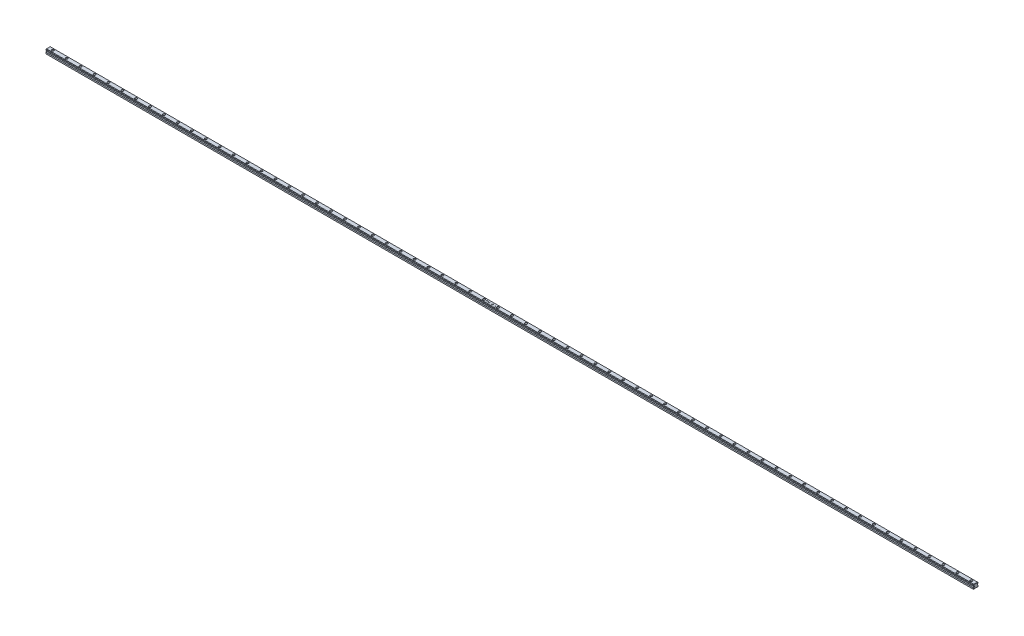
SolidWorks part; units mm, degrees
ref_plane "Front Plane" through (0, 0, 0) normal (0, 0, 1) x (1, 0, 0)
ref_plane "Top Plane" through (0, 0, 0) normal (0, 1, 0) x (1, 0, 0)
ref_plane "Right Plane" through (0, 0, 0) normal (1, 0, 0) x (0, 0, -1)
sketch "Sketch1" plane through (0, 0, 0) normal (1, 0, 0) x (0, 0, -1)
  line L0 (0, 0) -> (0, 33.316) construction
  line L1 (-7.9937, 26.9753) -> (8.0063, 26.9753)
  line L2 (8.0063, 26.9753) -> (10.0074, 24.9742)
  line L3 (10.0074, 24.9742) -> (10.0074, 22.0942)
  line L4 (10.0074, 22.0942) -> (7.4968, 19.5984)
  line L5 (7.4968, 19.5984) -> (7.4968, 17.5984)
  line L6 (7.4968, 17.5984) -> (10, 15.0953)
  line L7 (10, 15.0953) -> (10, 8.9753)
  line L8 (-10, 15.0953) -> (-10, 8.9753)
  line L9 (-7.4968, 17.5984) -> (-10, 15.0953)
  line L10 (-7.4843, 19.5984) -> (-7.4968, 17.5984)
  line L11 (-9.9948, 22.0942) -> (-7.4843, 19.5984)
  line L12 (-9.9948, 24.9742) -> (-9.9948, 22.0942)
  line L13 (-7.9937, 26.9753) -> (-9.9948, 24.9742)
  line L14 (-10, 8.9753) -> (10, 8.9753)
  dimension "D1" = 16
  dimension "D2" = 20
  dimension "D3" = 2.83
  dimension "D4" = 2.88
  dimension "D5" = 3.54
  dimension "D6" = 2
  dimension "D7" = 3.54
  dimension "D8" = 6.12
  dimension "D9" = 18
  dimension "D10" = 10
extrude "Boss-Extrude1" add sketch "Sketch1" along normal blind 4000
sketch "Sketch2" plane through (0, 26.9753, 0) normal (0, 1, 0) x (1, 0, 0)
  line L0 (4000, -10) -> (4000, 10) construction
  circle A0 centre (3980, 0) radius 4.75
  point P2 (4000, 0)
  dimension "D1" = 9.5
  dimension "D2" = 20
extrude "Cut-Extrude1" cut sketch "Sketch2" against normal blind 8.5
sketch "Sketch3" plane through (0, 18.4753, 0) normal (0, 1, 0) x (-1, 0, 0)
  circle A0 centre (-3980, 0) radius 3
  dimension "D1" = 6
extrude "Cut-Extrude2" cut sketch "Sketch3" against normal through all
pattern_linear "LPattern1" count 67 spacing 60 along (-1, 0, 0) of "Cut-Extrude1", "Cut-Extrude2"
sketch "Sketch4" plane through (0, 26.9753, 0) normal (0, 1, 0) x (1, 0, 0)
  text T0 "SHN 20 A " font "Century Gothic" height 3.5
extrude "Cut-Extrude3" cut sketch "Sketch4" against normal blind 2
chamfer "Chamfer1" distance 1 angle 45 28 edges at (0, 23.5342, 9.9948) (0, 20.8463, 8.7395) (0, 18.5984, 7.4905) (0, 16.3469, 8.7484) (0, 12.0353, 10) (0, 8.9753, 0) (0, 12.0353, -10) (0, 16.3469, -8.7484) (0, 18.5984, -7.4968) (0, 20.8463, -8.7521) (0, 23.5342, -10.0074) (0, 25.9747, -9.0069) (0, 26.9753, -0.0063) (0, 25.9747, 8.9943) (4000, 26.9753, -0.0063) (4000, 25.9747, -9.0069) (4000, 23.5342, -10.0074) (4000, 20.8463, -8.7521) (4000, 18.5984, -7.4968) (4000, 16.3469, -8.7484) (4000, 12.0353, -10) (4000, 8.9753, 0) (4000, 12.0353, 10) (4000, 16.3469, 8.7484) (4000, 18.5984, 7.4905) (4000, 20.8463, 8.7395) (4000, 23.5342, 9.9948) (4000, 25.9747, 8.9943)
